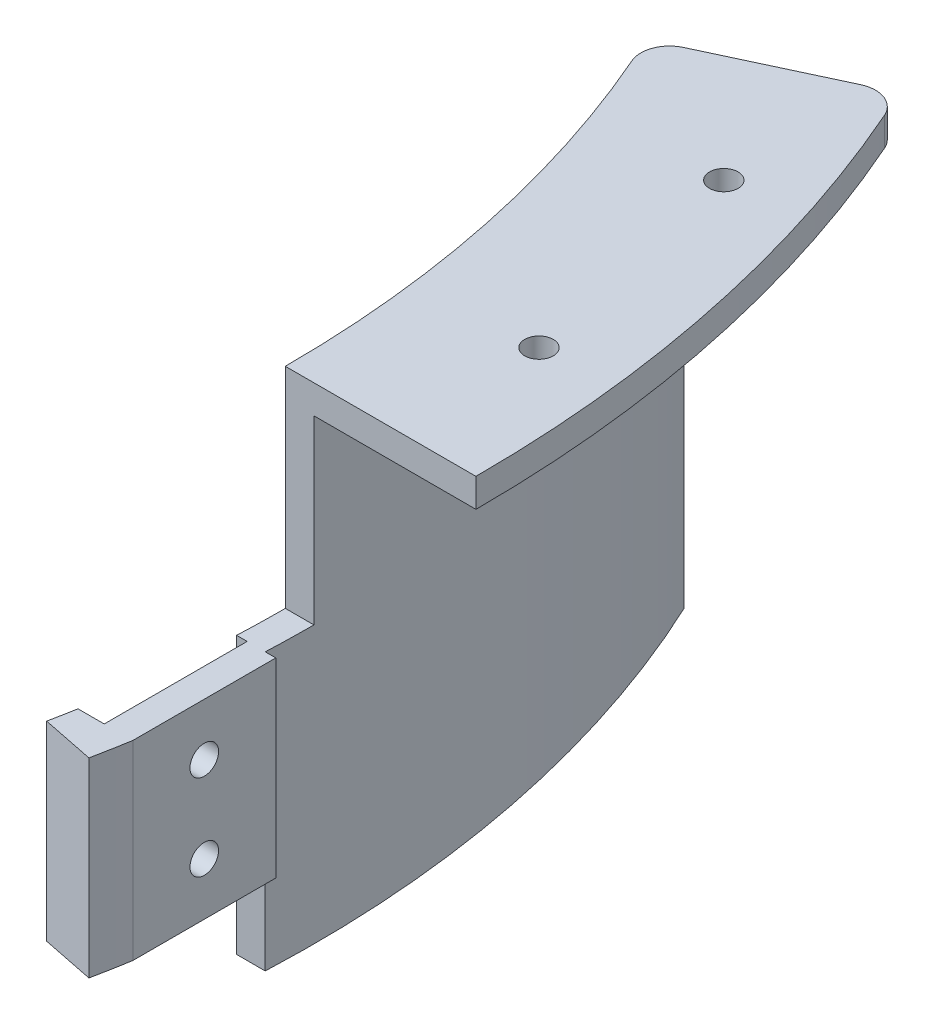
SolidWorks part; units mm, degrees
ref_plane "前视基准面" through (0, 0, 0) normal (0, 0, 1) x (1, 0, 0)
ref_plane "上视基准面" through (0, 0, 0) normal (0, 1, 0) x (1, 0, 0)
ref_plane "右视基准面" through (0, 0, 0) normal (1, 0, 0) x (0, 0, -1)
other "Configuration Table"
sketch "草图2" plane through (0, 0, 0) normal (0, 1, 0) x (1, 0, 0)
  line L0 (0, 0) -> (122.3516, 57.0535)
  line L2 (0, 0) -> (135, 0) construction
  line L3 (132.3289, -26.722) -> (0, 0)
  arc A0 (132.3289, -26.722) -> (122.3516, 57.0535) centre (0, 0) ccw
  dimension "D2" = 135
  dimension "D1" = 25
extrude "凸台-拉伸1" add sketch "草图2" against normal blind 64
sketch "草图3" plane through (0, 0, 0) normal (0, 1, 0) x (1, 0, 0)
  line L0 (0, 0) -> (104.2254, 48.6011)
  line L1 (122.3516, 57.0535) -> (0, 0) construction
  line L2 (0, 0) -> (112.7246, -22.7632)
  line L3 (0, 0) -> (132.3289, -26.722) construction
  arc A0 (112.7246, -22.7632) -> (104.2254, 48.6011) centre (0, 0) ccw
  dimension "D1" = 115
extrude "切除-拉伸1" cut sketch "草图3" against normal blind 64
sketch "草图4" plane through (0, 0, 0) normal (0, 1, 0) x (1, 0, 0)
  line L0 (0, 0) -> (135, 0) construction
  line L2 (113, -5) -> (116, -5)
  line L3 (113, -5) -> (113, -20)
  line L4 (113, -20) -> (116, -20)
  line L5 (116, -5) -> (116, -20)
  arc A0 (132.3289, -26.722) -> (122.3516, 57.0535) centre (0, 0) ccw construction
  point P11 (114.5, -5)
  dimension "D1" = 3
  dimension "D2" = 15
  dimension "D3" = 5
  dimension "D4" = 113
extrude "切除-拉伸2" cut sketch "草图4" against normal blind 84
sketch "草图5" plane through (0, -64, 0) normal (0, -1, 0) x (1, 0, 0)
  line L0 (132.3289, 26.722) -> (118.2814, 23.8853)
  line L1 (112.7246, 22.7632) -> (132.3289, 26.722) construction
  line L2 (106.9443, -49.869) -> (122.3516, -57.0535)
  line L4 (122.3516, -57.0535) -> (104.2254, -48.6011) construction
  line L6 (119, 20) -> (119, 5)
  line L7 (119, 5) -> (117.894, 5)
  line L9 (116, 5) -> (114.8913, 5) construction
  arc A0 (106.9443, -49.869) -> (117.894, 5) centre (0, 0) ccw
  arc A1 (122.3516, -57.0535) -> (132.3289, 26.722) centre (0, 0) ccw
  arc A4 (119, 20) -> (118.2814, 23.8853) centre (0, 0) ccw
  dimension "D1" = 118
  dimension "D2" = 3
  dimension "D3" = 15
extrude "切除-拉伸3" cut sketch "草图5" against normal blind 61
sketch "草图6" plane through (0, 0, 0) normal (0, 1, 0) x (1, 0, 0)
  line L0 (0, 0) -> (135, 0) construction
  line L1 (115, 0) -> (135, 0)
  line L2 (112.7246, -22.7632) -> (132.3289, -26.722)
  line L3 (112.7246, -22.7632) -> (132.3289, -26.722) construction
  line L4 (114.8913, -5) -> (116, -5)
  line L5 (116, -5) -> (116, -20)
  line L6 (116, -20) -> (113.2475, -20)
  arc A0 (132.3289, -26.722) -> (122.3516, 57.0535) centre (0, 0) ccw construction
  arc A1 (114.8913, -5) -> (104.2254, 48.6011) centre (0, 0) ccw construction
  arc A2 (112.7246, -22.7632) -> (113.2475, -20) centre (0, 0) ccw
  arc A3 (132.3289, -26.722) -> (135, 0) centre (0, 0) ccw
  arc A4 (114.8913, -5) -> (115, 0) centre (0, 0) ccw
  line M9 (114.8913, -5) -> (116, -5)
  line M10 (116, -5) -> (116, -20)
  line M11 (116, -20) -> (113.2475, -20)
  arc M12 (113.2475, -20) -> (112.7246, -22.7632) centre (0, 0) cw
  line M13 (112.7246, -22.7632) -> (132.3289, -26.722)
  arc M14 (132.3289, -26.722) -> (122.3516, 57.0535) centre (0, 0) ccw
  arc M16 (104.2254, 48.6011) -> (114.8913, -5) centre (0, 0) cw
  dimension "D2" = 135
extrude "切除-拉伸4" cut sketch "草图6" against normal blind 22 contours L1 M16 M9 M10 M11 M12 M13 M14
sketch "草图7" plane through (0, -64, 0) normal (0, -1, 0) x (1, 0, 0)
  line L0 (116, 5) -> (119, 5)
  line L1 (119, 5) -> (119, 20)
  line L3 (118.2814, 23.8853) -> (112.7246, 22.7632)
  line L5 (113.2475, 20) -> (116, 20)
  line L6 (116, 20) -> (116, 5)
  arc A0 (119, 20) -> (118.2814, 23.8853) centre (0, 0) ccw
  arc A1 (113.2475, 20) -> (112.7246, 22.7632) centre (0, 0) ccw
extrude "切除-拉伸5" cut sketch "草图7" against normal blind 22
fillet "圆角1" radius 3 1 edges at (122.3516, -1.5, -57.0535)
sketch "草图8" plane through (119, 0, 0) normal (1, 0, 0) x (0, 0, -1)
  line L0 (-23.8853, -32) -> (-5, -32) construction
  line L1 (-23.8853, -22) -> (-23.8853, -42) construction
  line L2 (-5, -22) -> (-5, -42) construction
  line L3 (-12.5, -22) -> (-12.5, -42) construction
  line L4 (-20, -22) -> (-5, -22) construction
  line L5 (-5, -42) -> (-20, -42) construction
  line L6 (-20, -22) -> (-20, -42) construction
  circle A0 centre (-12.5, -27.5) radius 1.5
  circle A1 centre (-12.5, -36.5) radius 1.5
  dimension "D1" = 3
  dimension "D2" = 3
  dimension "D3" = 9
  dimension "D4" = 4.5
  dimension "D5" = 7.5
extrude "切除-拉伸8" cut sketch "草图8" against normal blind 10
sketch "草图9" plane through (0, -64, 0) normal (0, -1, 0) x (1, 0, 0)
  line L1 (106.9443, -49.869) -> (104.2254, -48.6011)
  line L2 (117.894, 5) -> (114.8913, 5)
  arc A0 (106.9443, -49.869) -> (117.894, 5) centre (0, 0) ccw
  arc A1 (104.2254, -48.6011) -> (114.8913, 5) centre (0, 0) ccw
extrude "切除-拉伸9" cut sketch "草图9" against normal blind 13
sketch "草图10" plane through (0, 0, 0) normal (0, 1, 0) x (1, 0, 0)
  line L0 (119.6017, 55.7712) -> (104.2254, 48.6011) construction
  line L1 (115, 0) -> (135, 0) construction
  circle A0 centre (0, 0) radius 127.5 construction
  circle A1 centre (121.091, 39.915) radius 1.5
  circle A2 centre (126.6146, 15) radius 1.5
  dimension "D1" = 255
  dimension "D2" = 3
  dimension "D3" = 3
  dimension "D4" = 15
  dimension "D5" = 15
extrude "切除-拉伸10" cut sketch "草图10" against normal blind 10
fillet "圆角2" radius 3 1 edges at (104.2254, -25.5, -48.6011)
